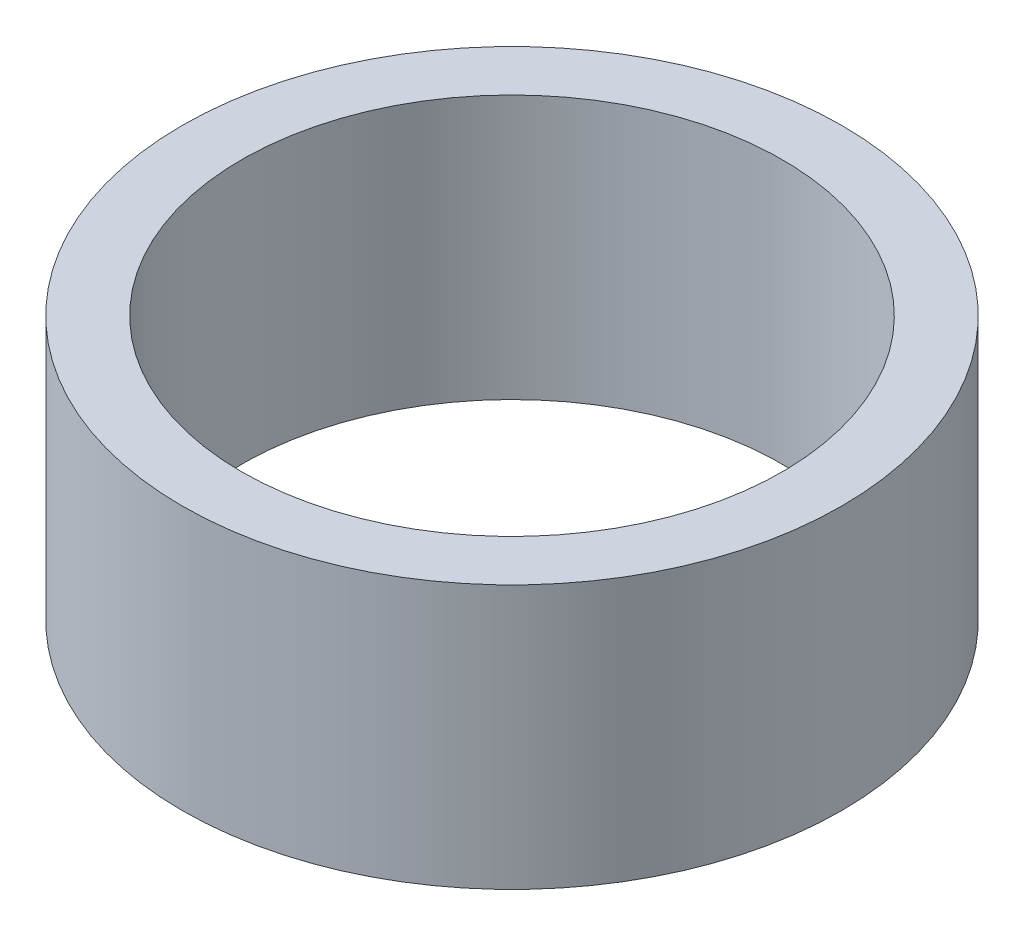
SolidWorks part; units mm, degrees
material "Plain Carbon Steel"
ref_plane "Front Plane" through (0, 0, 0) normal (0, 0, 1) x (1, 0, 0)
ref_plane "Top Plane" through (0, 0, 0) normal (0, 1, 0) x (1, 0, 0)
ref_plane "Right Plane" through (0, 0, 0) normal (1, 0, 0) x (0, 0, -1)
sketch "Sketch1" plane through (0, 0, 0) normal (0, 0, 1) x (1, 0, 0)
  line L0 (0, 0) -> (4.1, 0) construction
  line L1 (0, 13.0095) -> (0, -8.305) construction
  line L3 (4.1, 2) -> (5, 2)
  line L4 (4.1, 2) -> (4.1, -2)
  line L5 (4.1, -2) -> (5, -2)
  line L6 (5, 2) -> (5, -2)
  dimension "D1" = 8.2
  dimension "D2" = 10
  dimension "D3" = 4
revolve "Revolve1" add sketch "Sketch1" angle 360 about L1
